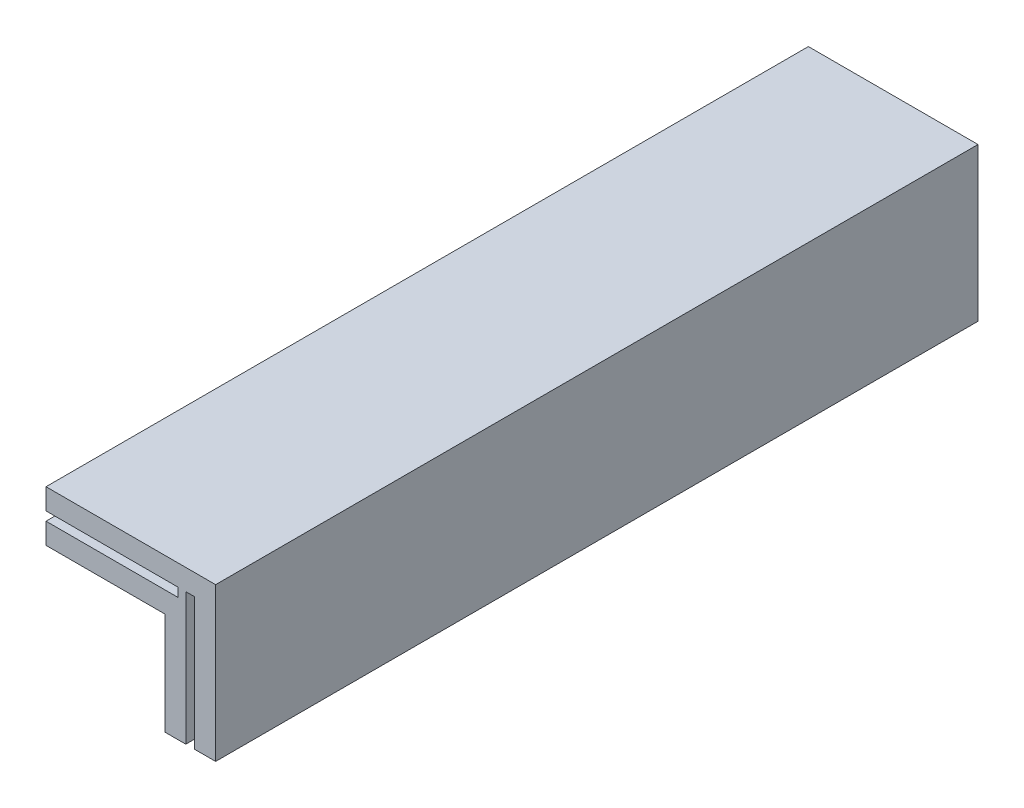
SolidWorks part; units mm, degrees
ref_plane "Front Plane" through (0, 0, 0) normal (0, 0, 1) x (1, 0, 0)
ref_plane "Top Plane" through (0, 0, 0) normal (0, 1, 0) x (1, 0, 0)
ref_plane "Right Plane" through (0, 0, 0) normal (1, 0, 0) x (0, 0, -1)
sketch "Sketch1" plane through (0, 0, 0) normal (0, 0, 1) x (1, 0, 0)
  line L0 (-1, 2.025) -> (1, 2.025)
  line L1 (-1, 4) -> (1, 4)
  line L2 (-1, 4) -> (-1, -4)
  line L3 (-1, -4) -> (1, -4)
  line L4 (1, 4) -> (1, -4)
  line L5 (-1, 4) -> (1, -4) construction
  line L6 (-1, -4) -> (1, 4) construction
  line L7 (-0.175, -4) -> (0.175, -4)
  line L8 (-0.175, -4) -> (-0.175, 1.2)
  line L9 (-0.175, 1.2) -> (0.175, 1.2)
  line L10 (0.175, -4) -> (0.175, 1.2)
  line L11 (-1, 0.025) -> (-5.675, 0.025)
  line L12 (-1, 0.025) -> (-1, 2.025)
  line L13 (-1, 2.025) -> (-5.675, 2.025)
  line L14 (-5.675, 0.025) -> (-5.675, 2.025)
  line L15 (-5.675, 0.85) -> (-0.475, 0.85)
  line L16 (-5.675, 0.85) -> (-5.675, 1.2)
  line L17 (-5.675, 1.2) -> (-0.475, 1.2)
  line L18 (-0.475, 0.85) -> (-0.475, 1.2)
  point P0 (0, 0)
  point P11 (0, 1.2)
  point P19 (-5.675, 1.025)
  point P20 (-0.475, 1.025)
  dimension "D1" = 0.35
  dimension "D2" = 5.2
  dimension "D3" = 8
  dimension "D4" = 2
  dimension "D5" = 5.2
  dimension "D6" = 2
  dimension "D7" = 0.35
  dimension "D8" = 0.3
extrude "Boss-Extrude1" add sketch "Sketch1" along normal blind 30 contours L14 L17 L2 L13 | L15 L14 L11 L12 | L18 L15 L12 L2 L3 L8 L9 L10 L4 L0 L17
